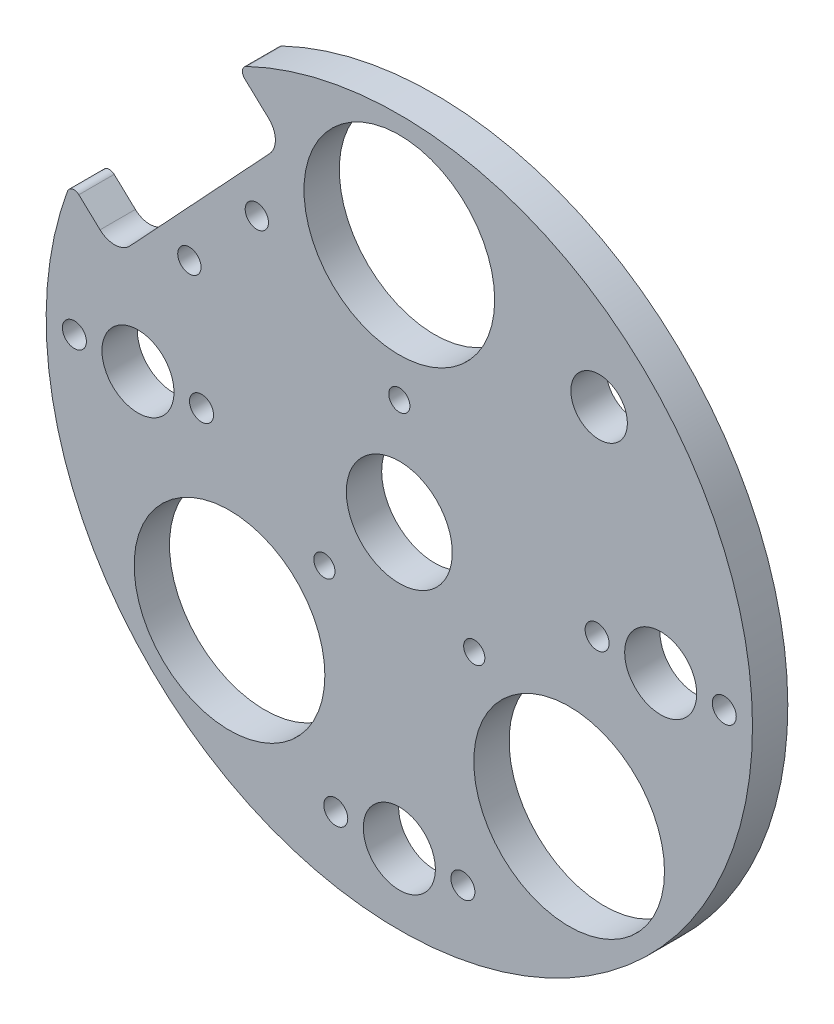
SolidWorks part; units mm, degrees
material "Acrylic (Medium-high impact)"
ref_plane "Front Plane" through (0, 0, 0) normal (0, 0, 1) x (1, 0, 0)
ref_plane "Top Plane" through (0, 0, 0) normal (0, 1, 0) x (1, 0, 0)
ref_plane "Right Plane" through (0, 0, 0) normal (1, 0, 0) x (0, 0, -1)
sketch "Sketch1" plane through (0, 0, 0) normal (0, 0, 1) x (1, 0, 0)
  circle A0 centre (0, 0) radius 50
  dimension "D1" = 100
extrude "Boss-Extrude1" add sketch "Sketch1" along normal blind 5
hole_wizard "Ø15.0 (15) Diameter Hole1" positions "Sketch3" profile "Sketch4" hole size "Ø15.0" standard "ISO" end condition through all
sketch "Sketch3" plane through (0, 0, 0) normal (0, 0, -1) x (-1, 0, 0)
  point P0 (0, 0)
sketch "Sketch4" plane through (0, 0, 0) normal (1, 0, 0) x (0, 1, 0)
  line L0 (0, 0) -> (0, 5)
  line L1 (0, 5) -> (7.5, 5)
  line L2 (7.5, 5) -> (7.5, 0)
  line L5 (7.5, 0) -> (0, 0)
  line L11 (0, -6.35) -> (0, 107.95) construction
  dimension "Thru Hole Dia." = 15
  dimension "Thru Hole Depth" = 5
hole_wizard "Ø10.2 (10.2) Diameter Hole1" positions "Sketch5" profile "Sketch6" hole size "Ø10.2" standard "ISO"
sketch "Sketch5" plane through (0, 0, 0) normal (0, 0, -1) x (-1, 0, 0)
  point P4 (37, 0)
  point P17 (-37, 0)
  point P18 (0, 0)
  point P21 (0, -37)
  point P23 (0, -40)
  dimension "D1" = 3
  dimension "D2" = 40
  dimension "D3" = 37
sketch "Sketch6" plane through (-37, 0, 0) normal (1, 0, 0) x (0, 1, 0)
  line L0 (0, 0) -> (0, 5)
  line L1 (0, 5) -> (5.1, 5)
  line L2 (5.1, 5) -> (5.1, 0)
  line L5 (5.1, 0) -> (0, 0)
  line L11 (0, -6.35) -> (0, 107.95) construction
  dimension "Thru Hole Dia." = 10.2
  dimension "Thru Hole Depth" = 5
hole_wizard "M3 Clearance Hole1" positions "Sketch7" profile "Sketch8" hole size "M3" standard "ISO" end condition through all
sketch "Sketch7" plane through (0, 0, 5) normal (0, 0, 1) x (1, 0, 0)
  circle A0 centre (37, 0) radius 5.1 construction
  circle A1 centre (0, -40) radius 5.1 construction
  point P0 (46, 0)
  point P2 (28, 0)
  point P11 (9, -40)
  point P13 (-9, -40)
  point P46 (-46, 0)
  point P47 (-28, 0)
  dimension "D2" = 9
  dimension "D1" = 9
  dimension "D4" = 9
  dimension "D5" = 9
  dimension "D6" = 2
  dimension "D3" = 40
sketch "Sketch8" plane through (46, 0, 5) normal (1, 0, 0) x (0, -1, 0)
  line L0 (0, 0) -> (0, 5)
  line L1 (0, 5) -> (1.7, 5)
  line L2 (1.7, 5) -> (1.7, 0)
  line L5 (1.7, 0) -> (0, 0)
  line L11 (0, -6.35) -> (0, 107.95) construction
  dimension "Thru Hole Dia." = 3.4
  dimension "Thru Hole Depth" = 5
sketch "Sketch9" plane through (0, 0, 5) normal (0, 0, 1) x (1, 0, 0)
  line L0 (0, 0) -> (24.0416, -24.0416) construction
  line L1 (0, 0) -> (71.3708, 0) construction
  circle A0 centre (24.0416, -24.0416) radius 13.5
  circle A1 centre (10.6066, -10.6066) radius 1.5
  circle A2 centre (-24.0416, -24.0416) radius 13.5
  circle A3 centre (-10.6066, -10.6066) radius 1.5
  circle A4 centre (0, 34) radius 13.5
  circle A5 centre (0, 15) radius 1.5
  point P13 (0, 0)
  dimension "D1" = 27
  dimension "D3" = 45
  dimension "D4" = 3
  dimension "D5" = 19
  dimension "D7" = 27
  dimension "D9" = 3
  dimension "D10" = 19
  dimension "D2" = 34
  dimension "D8" = 34
  dimension "D6" = 2
extrude "Cut-Extrude1" cut sketch "Sketch9" against normal blind 10
sketch "Sketch10" plane through (0, 0, 5) normal (0, 0, 1) x (1, 0, 0)
  line L0 (-27.2748, 48.4556) -> (-18.4986, 40.2716)
  line L5 (-18.3505, 36.0316) -> (-38.1285, 14.8223)
  line L6 (-42.3685, 14.6743) -> (-51.1448, 22.8582)
  line L7 (-51.1448, 22.8582) -> (-27.2748, 48.4556)
  line L8 (0, 0) -> (-28.2395, 25.427) construction
  line L9 (-40.1745, 12.6283) -> (-10.2788, 12.6283) construction
  circle A0 centre (-20.1744, 27.4774) radius 1.65
  circle A1 centre (-29.7224, 17.2385) radius 1.65
  arc A2 (-42.3685, 14.6743) -> (-38.1285, 14.8223) centre (-40.3225, 16.8683) ccw
  arc A3 (-18.4986, 40.2716) -> (-18.3505, 36.0316) centre (-20.5446, 38.0776) cw
  point P17 (-16.3045, 38.2257)
  dimension "D6" = 3.3
  dimension "D7" = 3.3
  dimension "D12" = 3
  dimension "D1" = 15
  dimension "D2" = 35
  dimension "D3" = 38
  dimension "D4" = 47
  dimension "D5" = 138
  dimension "D8" = 4.5
  dimension "D9" = 10.5
  dimension "D10" = 10.5
  dimension "D11" = 4.5
extrude "Cut-Extrude2" cut sketch "Sketch10" against normal blind 10
sketch "Sketch13" plane through (0, 0, 5) normal (0, 0, 1) x (1, 0, 0)
  line L0 (0, 0) -> (28.2843, 28.2843) construction
  line L1 (0, 0) -> (21.835, 0) construction
  circle A0 centre (28.2843, 28.2843) radius 4
  dimension "D1" = 8
  dimension "D2" = 40
  dimension "D3" = 45
extrude "Cut-Extrude6" cut sketch "Sketch13" against normal blind 10
fillet "Fillet1" radius 1 2 edges at (-46.4569, 18.4867, 2.5) (-22.9494, 44.4221, 2.5)
